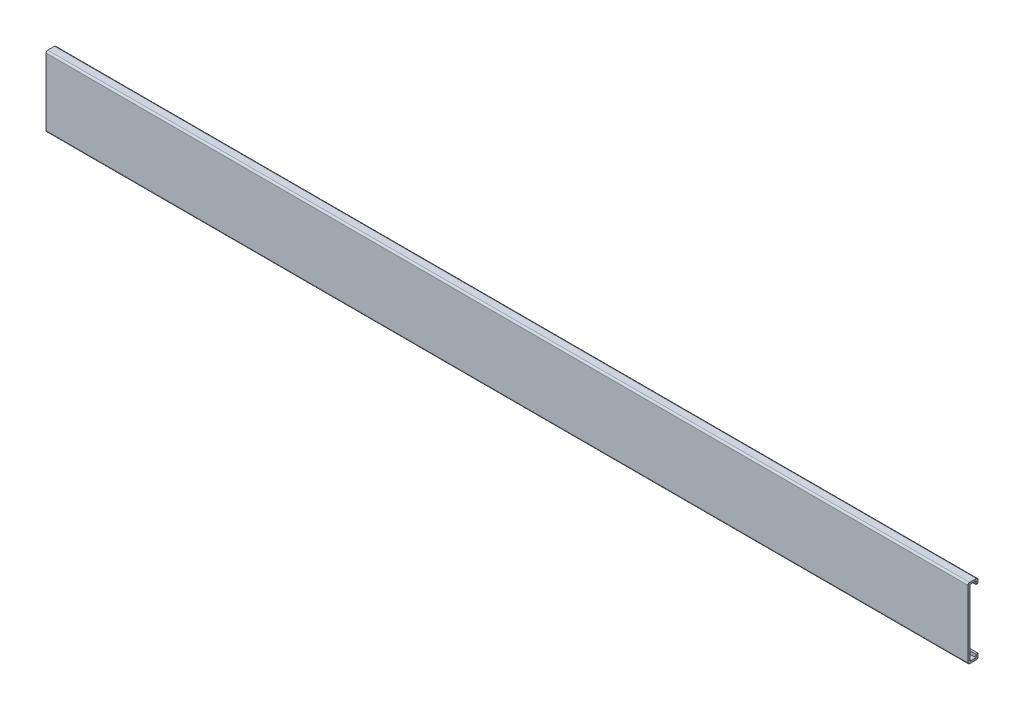
SolidWorks part; units mm, degrees
ref_plane "Спереди" through (0, 0, 0) normal (0, 0, 1) x (1, 0, 0)
ref_plane "Сверху" through (0, 0, 0) normal (0, 1, 0) x (1, 0, 0)
ref_plane "Справа" through (0, 0, 0) normal (1, 0, 0) x (0, 0, -1)
sketch "Эскиз1" plane through (0, 0, 0) normal (1, 0, 0) x (0, 0, -1)
  line L0 (0, -20) -> (0, 20)
  line L1 (-12.4481, 0) -> (26.4522, 0) construction
  line L2 (1, 21) -> (5, 21)
  line L3 (6, 20) -> (6, 18)
  line L4 (6, -20) -> (6, -18)
  line L5 (1, -21) -> (5, -21)
  arc A0 (5, 21) -> (6, 20) centre (5, 20) cw
  arc A1 (0, 20) -> (1, 21) centre (1, 20) cw
  arc A2 (0, -20) -> (1, -21) centre (1, -20) ccw
  arc A3 (5, -21) -> (6, -20) centre (5, -20) ccw
  point P0 (0, -21)
  point P11 (0, 21)
  point P20 (0, 0)
  dimension "D1" = 1
extrude "Вытянуть-Тонкостенный3" add sketch "Эскиз1" along normal blind 550 thin
